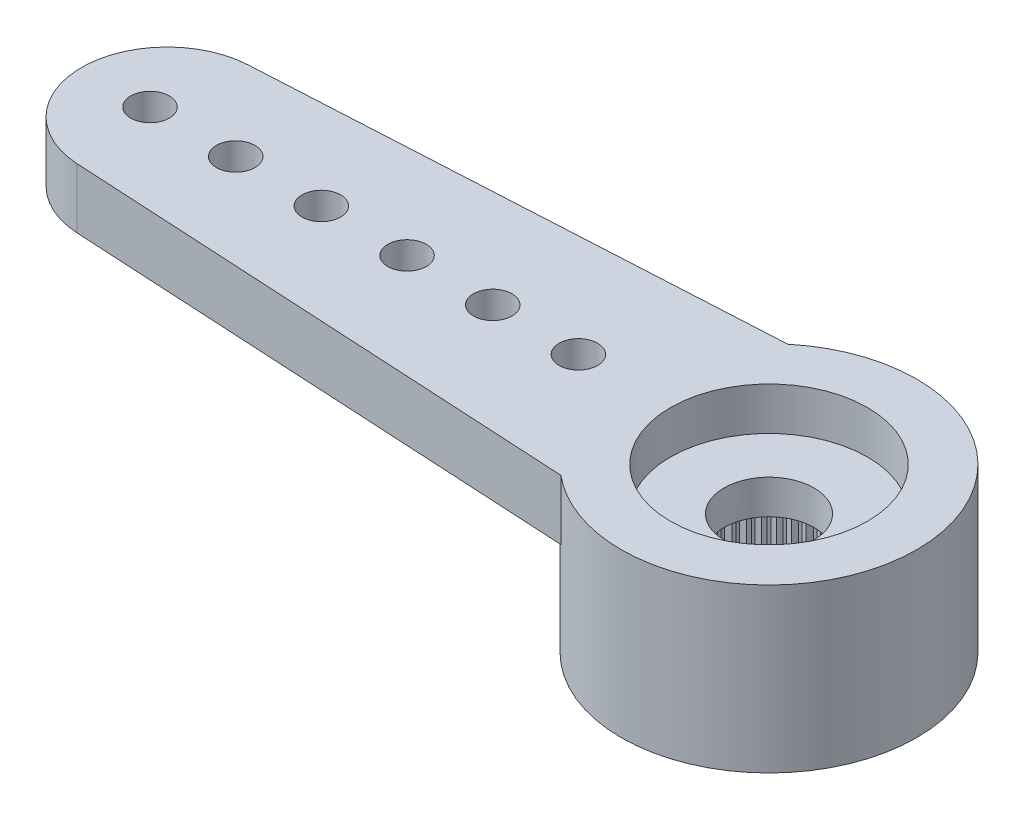
SolidWorks part; units mm, degrees
material "PVC Rígido"
ref_plane "Plano frontal" through (0, 0, 0) normal (0, 0, 1) x (1, 0, 0)
ref_plane "Plano superior" through (0, 0, 0) normal (0, 1, 0) x (1, 0, 0)
ref_plane "Plano direito" through (0, 0, 0) normal (1, 0, 0) x (0, 0, -1)
sketch "Esboço1" plane through (0, 0, 0) normal (0, 1, 0) x (1, 0, 0)
  line L0 (0, 0) -> (-14.05, 0) construction
  line L1 (-14.1591, 1.997) -> (-2.2091, 2.65)
  line L2 (-2.2091, -2.65) -> (-14.1591, -1.997)
  arc A0 (-2.2091, -2.65) -> (-2.2091, 2.65) centre (0, 0) ccw
  arc A1 (-14.1591, 1.997) -> (-14.1591, -1.997) centre (-14.05, 0) ccw
  dimension "D1" = 6.9
  dimension "D2" = 4
  dimension "D3" = 19.5
  dimension "D4" = 5.3
extrude "Ressalto-extrusão1" add sketch "Esboço1" against normal blind 1.4
sketch "Esboço2" plane through (0, -1.4, 0) normal (0, -1, 0) x (1, 0, 0)
  arc A0 (-2.2091, -2.65) -> (-2.2091, 2.65) centre (0, 0) ccw construction
  circle A1 centre (0, 0) radius 3.45
extrude "Ressalto-extrusão2" add sketch "Esboço2" along normal offset from surface (2.4 mm away) 3.8 up to face at (-7.242, 0, 0)
hole_wizard "Furo4" positions "Esboço9" profile "Esboço10" legacy end condition through all
sketch "Esboço9" plane through (0, 0, 0) normal (0, 1, 0) x (1, 0, 0)
  line L1 (-14.45, 0) -> (0, 0) construction
  arc A2 (-14.1591, 1.997) -> (-14.1591, -1.997) centre (-14.05, 0) ccw construction
  point P0 (-14.45, 0)
  point P19 (-16.05, 0)
  dimension "D1" = 1.6
sketch "Esboço10" plane through (-14.45, 0, 0) normal (1, 0, 0) x (0, 0, 1)
  line L0 (0, 0) -> (0, 3.8)
  line L1 (0, 3.8) -> (0.45, 3.8)
  line L2 (0.45, 3.8) -> (0.45, 0)
  line L3 (0.45, 0) -> (0, 0)
  line L4 (0, 110) -> (0, -10) construction
  dimension "Diameter" = 0.9
  dimension "Depth" = 3.8
pattern_linear "Padrão linear1" count 6 spacing 2 along (1, 0, 0) of "Furo4"
hole_wizard "Furo1" positions "Esboço3" profile "Esboço4" legacy
sketch "Esboço3" plane through (0, -3.8, 0) normal (0, -1, 0) x (-1, 0, 0)
  point P0 (0, 0)
sketch "Esboço4" plane through (0, -3.8, 0) normal (1, 0, 0) x (0, 0, -1)
  line L0 (0, 0) -> (0, 2)
  line L1 (0, 2) -> (2.475, 2)
  line L2 (2.475, 2) -> (2.475, 0)
  line L3 (2.475, 0) -> (0, 0)
  line L4 (0, 110) -> (0, -10) construction
  dimension "Diameter" = 4.95
  dimension "Depth" = 2
hole_wizard "Furo2" positions "Esboço5" profile "Esboço6" legacy
sketch "Esboço5" plane through (0, 0, 0) normal (0, 1, 0) x (1, 0, 0)
  point P0 (0, 0)
sketch "Esboço6" plane through (0, 0, 0) normal (1, 0, 0) x (0, 0, 1)
  line L0 (0, 0) -> (0, 1)
  line L1 (0, 1) -> (2.3, 1)
  line L2 (2.3, 1) -> (2.3, 0)
  line L3 (2.3, 0) -> (0, 0)
  line L4 (0, 110) -> (0, -10) construction
  dimension "Diameter" = 4.6
  dimension "Depth" = 1
hole_wizard "Furo3" positions "Esboço7" profile "Esboço8" legacy end condition through all
sketch "Esboço7" plane through (0, 0, 0) normal (0, 1, 0) x (1, 0, 0)
  point P0 (0, 0)
sketch "Esboço8" plane through (0, 0, 0) normal (1, 0, 0) x (0, 0, 1)
  line L0 (0, 0) -> (0, 3.8)
  line L1 (0, 3.8) -> (1.05, 3.8)
  line L2 (1.05, 3.8) -> (1.05, 0)
  line L3 (1.05, 0) -> (0, 0)
  line L4 (0, 110) -> (0, -10) construction
  dimension "Diameter" = 2.1
  dimension "Depth" = 3.8
sketch "Esboço11" plane through (0, -3.8, 0) normal (0, -1, 0) x (1, 0, 0)
  line L0 (-0.0981, 2.4731) -> (0, 2.375)
  line L1 (0, 2.375) -> (0.0981, 2.4731)
  line L2 (0, 0) -> (0, 2.475) construction
  circle A0 centre (0, 0) radius 2.375 construction
  circle A1 centre (0, 0) radius 2.475
  arc A2 (0.0981, 2.4731) -> (-0.0981, 2.4731) centre (0, 0) ccw
  dimension "D3" = 4.75
  dimension "D2" = 0.1
  dimension "D1" = 0
extrude "Ressalto-extrusão3" add sketch "Esboço11" against normal up to surface (2 mm away) up to face at (0, -1.8, 1.05)
pattern_circular "PadrãoCircular1" count 60 over 360 about axis through (0, 0, 0) along (0, 1, 0) of "Ressalto-extrusão3"
